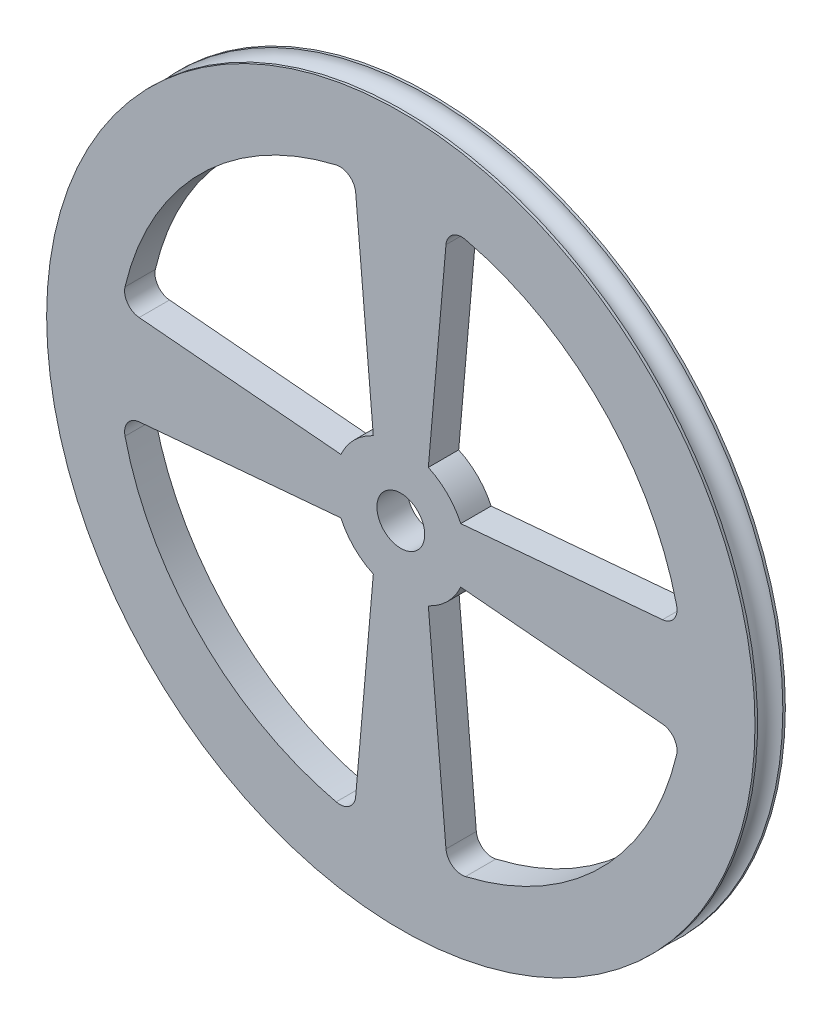
SolidWorks part; units mm, degrees
ref_plane "Front Plane" through (0, 0, 0) normal (0, 0, 1) x (1, 0, 0)
ref_plane "Top Plane" through (0, 0, 0) normal (0, 1, 0) x (1, 0, 0)
ref_plane "Right Plane" through (0, 0, 0) normal (1, 0, 0) x (0, 0, -1)
sketch "Sketch1" plane through (0, 0, 0) normal (0, 0, 1) x (1, 0, 0)
  line L0 (7.5224, -3.4521) -> (35.0637, -5.8617)
  line L1 (3.4521, 7.5224) -> (5.8617, 35.0637)
  line L2 (-3.4521, 7.5224) -> (-5.8617, 35.0637)
  line L3 (7.5224, 3.4521) -> (35.0637, 5.8617)
  line L4 (-3.4521, -7.5224) -> (-5.8617, -35.0637)
  line L5 (3.4521, -7.5224) -> (5.8617, -35.0637)
  line L8 (-7.5224, -3.4521) -> (-35.0637, -5.8617)
  line L9 (-7.5224, 3.4521) -> (-35.0637, 5.8617)
  arc A0 (5.8617, -35.0637) -> (35.0637, -5.8617) centre (0, 0) ccw
  circle A1 centre (0, 0) radius 3
  arc A2 (-7.5224, -3.4521) -> (-3.4521, -7.5224) centre (0, 0) ccw
  arc A3 (-35.0637, -5.8617) -> (-5.8617, -35.0637) centre (0, 0) ccw
  arc A5 (35.0637, 5.8617) -> (5.8617, 35.0637) centre (0, 0) ccw
  arc A6 (-5.8617, 35.0637) -> (-35.0637, 5.8617) centre (0, 0) ccw
  arc A7 (-3.4521, 7.5224) -> (-7.5224, 3.4521) centre (0, 0) ccw
  arc A8 (7.5224, 3.4521) -> (3.4521, 7.5224) centre (0, 0) ccw
  arc A9 (3.4521, -7.5224) -> (7.5224, -3.4521) centre (0, 0) ccw
  circle A10 centre (0, 0) radius 44.45
  point P27 (0, 0)
extrude "Boss-Extrude1" add sketch "Sketch1" along normal blind 3.81
fillet "Fillet1" radius 2 2 edges at (35.0637, -5.8617, 1.905) (35.0637, 5.8617, 1.905)
fillet "Fillet2" radius 2 6 edges at (5.8617, 35.0637, 1.905) (-5.8617, 35.0637, 1.905) (-35.0637, 5.8617, 1.905) (-35.0637, -5.8617, 1.905) (-5.8617, -35.0637, 1.905) (5.8617, -35.0637, 1.905)
sketch "Sketch3" plane through (0, 0, 0) normal (0, 1, 0) x (1, 0, 0)
  line L0 (-44.45, 0) -> (-44.45, -3.81) construction
  line L1 (0, 0) -> (0, -27.5045)
  circle A0 centre (-44.45, -1.905) radius 1.5875
revolve "Cut-Revolve1" cut sketch "Sketch3" angle 360 about L1
